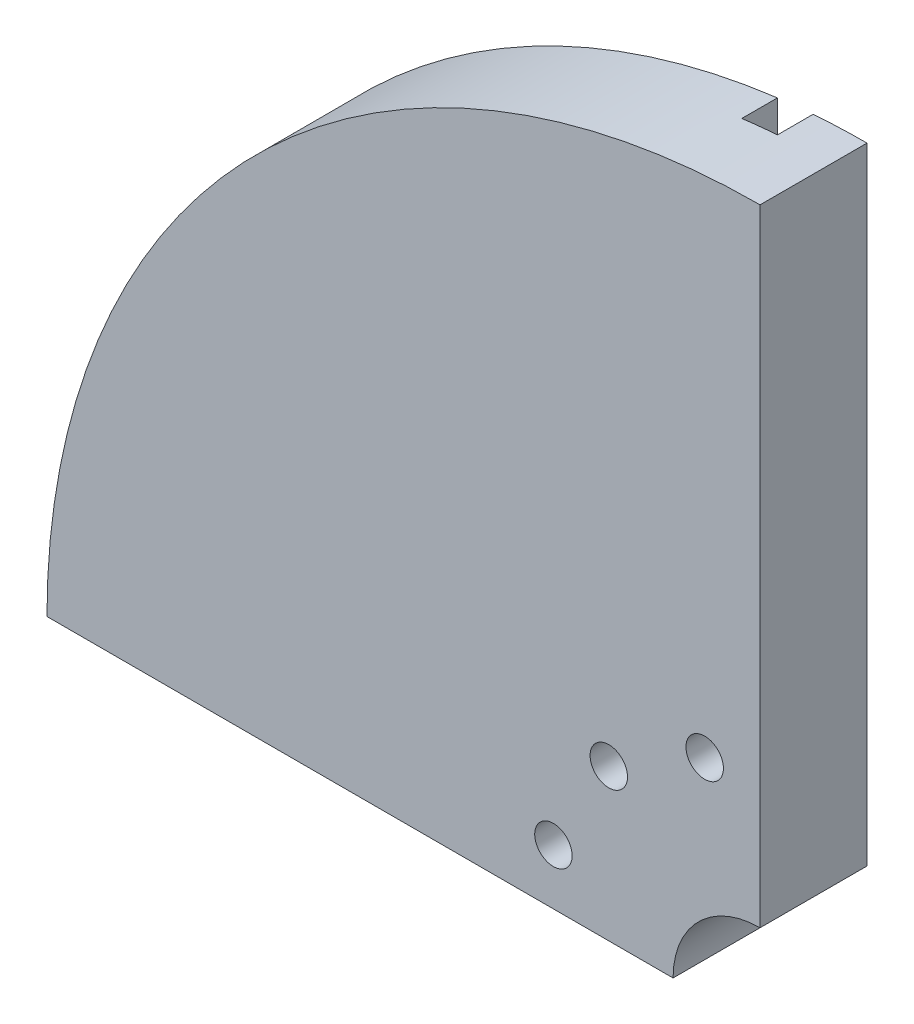
SolidWorks part; units mm, degrees
ref_plane "Front Plane" through (0, 0, 0) normal (0, 0, 1) x (1, 0, 0)
ref_plane "Top Plane" through (0, 0, 0) normal (0, 1, 0) x (1, 0, 0)
ref_plane "Right Plane" through (0, 0, 0) normal (1, 0, 0) x (0, 0, -1)
sketch "Sketch1" plane through (0, 0, 0) normal (0, 0, 1) x (1, 0, 0)
  line L0 (0, 100) -> (0, 0)
  line L1 (0, 0) -> (-100, 0)
  arc A0 (0, 100) -> (-100, 0) centre (0, 0) ccw
  dimension "D1" = 100
extrude "Boss-Extrude1" add sketch "Sketch1" along normal blind 15
sketch "Sketch2" plane through (0, 0, 0) normal (0, 0, 1) x (1, 0, 0)
  line L0 (0, 0) -> (-7.7646, 28.9778) construction
  line L1 (0, 0) -> (-21.2132, 21.2132) construction
  line L2 (0, 0) -> (-34.9836, 9.1821) construction
  circle A3 centre (-7.7646, 28.9778) radius 2.625
  circle A4 centre (-21.2132, 21.2132) radius 2.625
  circle A5 centre (-28.9778, 7.7646) radius 2.625
  point P14 (0, 0)
  dimension "D1" = 5.25
  dimension "D2" = 3
extrude "Cut-Extrude1" cut sketch "Sketch2" along normal through all
sketch "Sketch3" plane through (0, 0, 0) normal (0, 0, 1) x (1, 0, 0)
  circle A0 centre (0, 0) radius 12.2
  dimension "D1" = 24.4
extrude "Cut-Extrude2" cut sketch "Sketch3" along normal blind 20
sketch "Sketch5" plane through (0, 0, 0) normal (0, 0, 1) x (1, 0, 0)
  line L5 (-71.9587, 20.8267) -> (-61.1157, 11.7283)
  line L6 (-58.5632, 10.4606) -> (-47.7202, 1.3622)
  line L10 (-58.5632, 10.4606) -> (-12.0876, 65.8482)
  line L11 (-12.0876, 65.8482) -> (-1.2445, 56.7498)
  line L16 (-47.7202, 1.3622) -> (-1.2445, 56.7498)
  line L25 (-71.9587, 20.8267) -> (-25.4831, 76.2143)
  line L26 (-25.4831, 76.2143) -> (-14.64, 67.1159)
  line L27 (-61.1157, 11.7283) -> (-14.64, 67.1159)
  line L31 (-85.7132, 31.8965) -> (-74.8701, 22.7981)
  line L32 (-85.7132, 31.8965) -> (-39.2375, 87.2841)
  line L33 (-39.2375, 87.2841) -> (-28.3944, 78.1857)
  line L34 (-74.8701, 22.7981) -> (-28.3944, 78.1857)
  point P5 (0, 0)
  point P6 (-0.3371, 85.6373)
  point P11 (0, 0)
  point P12 (0, 0)
  point P17 (0, 0)
  point P18 (0.1756, -0.1781)
  point P31 (0, 0)
  point P32 (0, 0)
  point P33 (0, 0)
extrude "Cut-Extrude5" cut sketch "Sketch5" along normal blind 10
sketch "Sketch6" plane through (0, 0, 0) normal (0, 0, 1) x (1, 0, 0)
  line L16 (-16.9594, 74.4195) -> (-16.9594, 94.4195)
  line L21 (-93.6705, 16.9005) -> (-73.6705, 16.9005)
  line L22 (-93.6705, 16.9005) -> (-93.6705, 2.9005)
  line L23 (-16.9594, 74.4195) -> (-2.9594, 74.4195)
  line L24 (-2.9594, 74.4195) -> (-2.9594, 94.4195)
  line L25 (-16.9594, 94.4195) -> (-2.9594, 94.4195)
  line L26 (-16.9594, 74.4195) -> (-2.9594, 94.4195) construction
  line L27 (-2.9594, 74.4195) -> (-16.9594, 94.4195) construction
  line L32 (-93.6705, 2.9005) -> (-73.6705, 2.9005)
  line L33 (-73.6705, 16.9005) -> (-73.6705, 2.9005)
  line L38 (-93.6705, 16.9005) -> (-73.6705, 2.9005) construction
  line L39 (-93.6705, 2.9005) -> (-73.6705, 16.9005) construction
  point P0 (-83.6705, 9.9005)
  point P5 (0, 0)
  point P6 (0, 0)
  point P7 (0, 0)
  point P8 (0, 0)
  point P9 (0, 0)
  point P10 (0, 0)
  point P11 (0, 0)
  point P12 (0, 0)
  point P13 (0, 0)
  point P14 (0, 0)
  point P16 (-9.9594, 84.4195)
  dimension "D1" = 14
  dimension "D2" = 20
  dimension "D3" = 14
  dimension "D4" = 20
extrude "Cut-Extrude6" cut sketch "Sketch6" along normal blind 10
sketch "Sketch8" plane through (0, 0, 0) normal (0, 0, 1) x (1, 0, 0)
  line L0 (-43.5998, 8.8315) -> (-89.404, 46.905)
  line L1 (-43.5998, 8.8315) -> (-46.2607, 4.5983)
  line L2 (-89.404, 46.905) -> (-92.0648, 42.6718)
  line L3 (-46.2607, 4.5983) -> (-92.0648, 42.6718)
  line L9 (-91.2597, 6.9249) -> (-91.2597, 11.9249)
  line L10 (-91.2597, 6.9249) -> (-101.2597, 6.9249)
  line L11 (-101.2597, 6.9249) -> (-101.2597, 11.9249)
  line L12 (-91.2597, 11.9249) -> (-101.2597, 11.9249)
  line L13 (-91.2597, 6.9249) -> (-101.2597, 11.9249) construction
  line L14 (-101.2597, 6.9249) -> (-91.2597, 11.9249) construction
  line L15 (-12.5619, 102.0561) -> (-12.5619, 92.0561)
  line L16 (-12.5619, 102.0561) -> (-7.5619, 102.0561)
  line L17 (-7.5619, 102.0561) -> (-7.5619, 92.0561)
  line L18 (-12.5619, 92.0561) -> (-7.5619, 92.0561)
  line L19 (-12.5619, 102.0561) -> (-7.5619, 92.0561) construction
  line L20 (-7.5619, 102.0561) -> (-12.5619, 92.0561) construction
  point P0 (-96.2597, 9.4249)
  point P11 (-10.0619, 97.0561)
  dimension "D1" = 10
  dimension "D2" = 5
  dimension "D3" = 10
  dimension "D4" = 5
  dimension "D5" = 5
extrude "Cut-Extrude7" cut sketch "Sketch8" along normal blind 5
